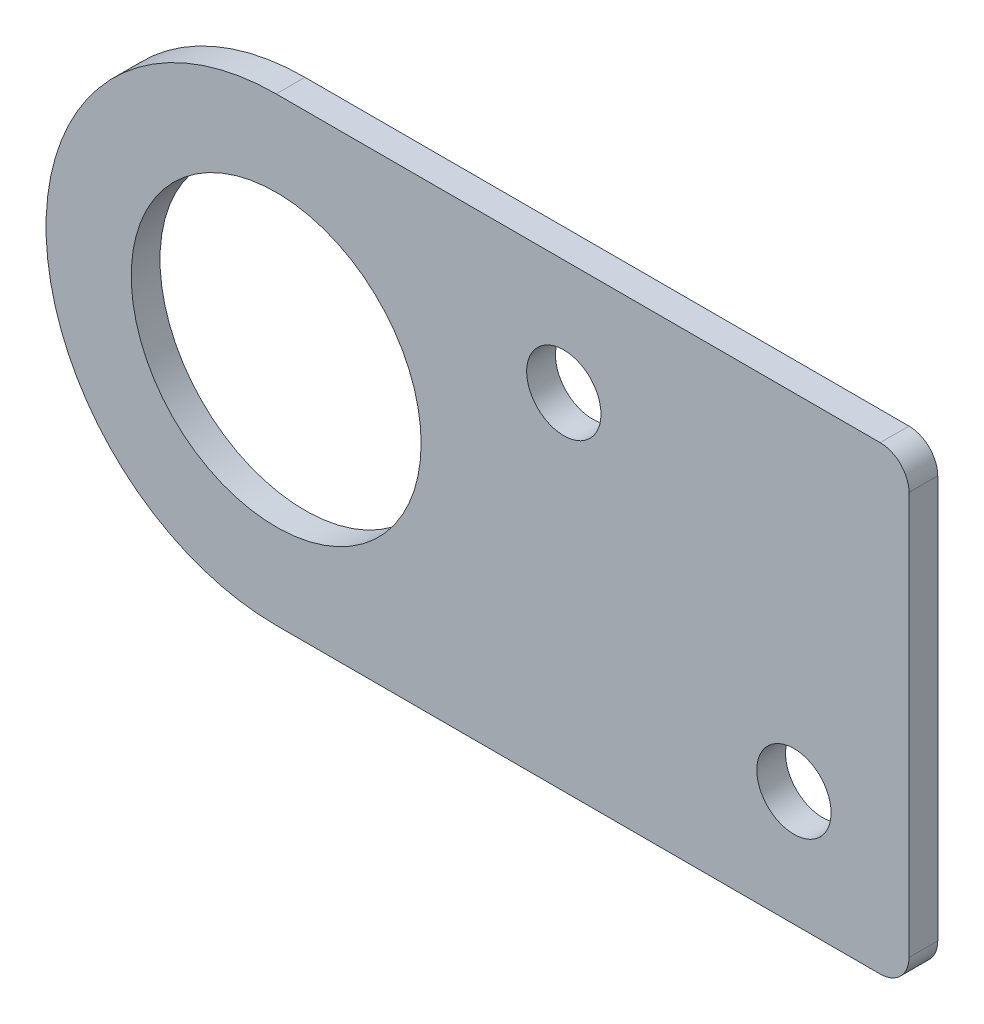
SolidWorks part; units mm, degrees
ref_plane "Front Plane" through (0, 0, 0) normal (0, 0, 1) x (1, 0, 0)
ref_plane "Top Plane" through (0, 0, 0) normal (0, 1, 0) x (1, 0, 0)
ref_plane "Right Plane" through (0, 0, 0) normal (1, 0, 0) x (0, 0, -1)
sketch "Sketch1" plane through (0, 0, 0) normal (0, 0, 1) x (1, 0, 0)
  line L0 (-174.625, 12.7) -> (-139.7, 12.7)
  line L1 (165.1, -12.7) -> (-165.1, -12.7)
  line L2 (165.1, -12.7) -> (165.1, 12.7)
  line L3 (165.1, 12.7) -> (-165.1, 12.7)
  line L4 (-165.1, -12.7) -> (-165.1, 12.7)
  line L5 (165.1, -12.7) -> (-165.1, 12.7) construction
  line L6 (165.1, 12.7) -> (-165.1, -12.7) construction
  line L7 (-139.7, 12.7) -> (-139.7, -12.7)
  line L8 (-139.7, -12.7) -> (-174.625, -12.7)
  line L9 (-165.1, 11.1125) -> (-88.6699, 11.1125) construction
  line L10 (-174.625, 12.7) -> (-174.625, 8) construction
  line L11 (0, 12.7) -> (0, -12.7) construction
  line L12 (139.7, 12.7) -> (139.7, -12.7)
  line L13 (165.1, 12.7) -> (177.4902, 15.4878)
  line L14 (165.1, -12.7) -> (177.4902, -15.4878)
  circle A0 centre (-174.625, 0) radius 8
  circle A1 centre (-174.625, 0) radius 12.7
  circle A2 centre (-158.75, 6.35) radius 2.05
  circle A3 centre (-146.05, -6.35) radius 2.05
  circle A7 centre (180.975, 0) radius 11.1125
  circle A8 centre (180.975, 0) radius 15.875
  circle A9 centre (146.05, -6.35) radius 2.05
  circle A10 centre (158.75, 6.35) radius 2.05
  point P0 (0, 0)
  dimension "D3" = 16
  dimension "D6" = 4.1
  dimension "D12" = 22.225
  dimension "D14" = 31.75
  dimension "D1" = 330.2
  dimension "D2" = 25.4
  dimension "D4" = 174.625
  dimension "D5" = 25.4
  dimension "D7" = 6.35
  dimension "D8" = 1.5875
  dimension "D9" = 6.35
  dimension "D10" = 6.35
  dimension "D11" = 6.35
  dimension "D13" = 180.975
extrude "Boss-Extrude1" add sketch "Sketch1" along normal blind 1.5875
fillet "Fillet1" radius 1.5875 2 edges at (-139.7, -12.7, 0.7937) (-139.7, 12.7, 0.7937)
